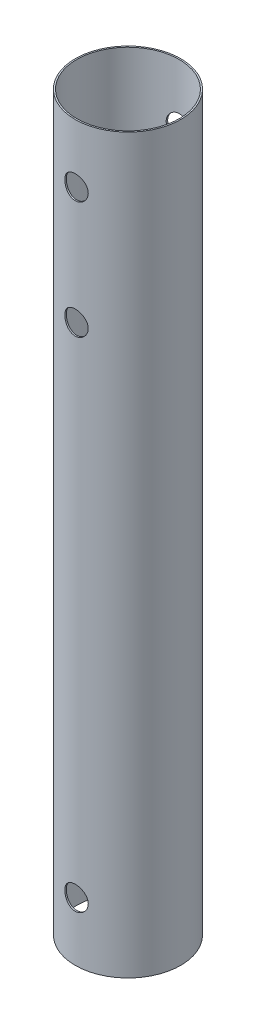
SolidWorks part; units mm, degrees
ref_plane "Front Plane" through (0, 0, 0) normal (0, 0, 1) x (1, 0, 0)
ref_plane "Top Plane" through (0, 0, 0) normal (0, 1, 0) x (1, 0, 0)
ref_plane "Right Plane" through (0, 0, 0) normal (1, 0, 0) x (0, 0, -1)
sketch "Sketch1" plane through (0, 0, 0) normal (0, 1, 0) x (1, 0, 0)
  circle A0 centre (0, 0) radius 9
  circle A1 centre (0, 0) radius 8.75
  dimension "D1" = 18
  dimension "D2" = 17.5
extrude "Boss-Extrude1" add sketch "Sketch1" along normal blind 125
sketch "Sketch2" plane through (0, 0, 0) normal (0, 0, 1) x (1, 0, 0)
  line L0 (8.75, 125) -> (-8.75, 125) construction
  circle A0 centre (0, 95) radius 2
  circle A1 centre (0, 115) radius 2
  circle A2 centre (0, 10) radius 2
  dimension "D1" = 4
  dimension "D2" = 4
  dimension "D3" = 4
  dimension "D4" = 30
  dimension "D5" = 20
  dimension "D6" = 10
extrude "Cut-Extrude1" cut sketch "Sketch2" against normal through all both and the other way through all
